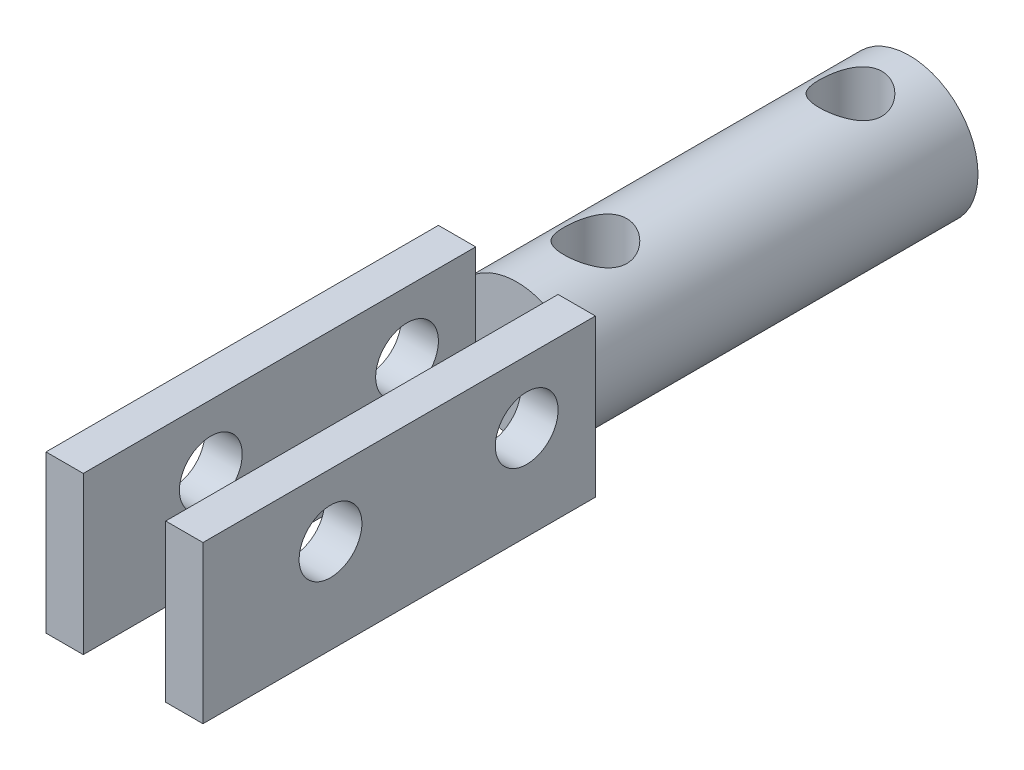
SolidWorks part; units mm, degrees
ref_plane "Plan de face" through (0, 0, 0) normal (0, 0, 1) x (1, 0, 0)
ref_plane "Plan de dessus" through (0, 0, 0) normal (0, 1, 0) x (1, 0, 0)
ref_plane "Plan de droite" through (0, 0, 0) normal (1, 0, 0) x (0, 0, -1)
sketch "Sketch1" plane through (0, 0, 0) normal (0, 0, 1) x (1, 0, 0)
  circle A0 centre (0, 0) radius 3.5
  dimension "D1" = 7
extrude "Boss-Extrude1" add sketch "Sketch1" along normal blind 20
sketch "Sketch2" plane through (0, 0, 0) normal (0, 1, 0) x (1, 0, 0)
  line L0 (3.5, 0) -> (-3.5, 0) construction
  circle A0 centre (0, -3) radius 1.6
  circle A1 centre (0, -16) radius 1.6
  dimension "D1" = 3.2
  dimension "D2" = 3.2
  dimension "D3" = 3
  dimension "D4" = 13
extrude "Cut-Extrude1" cut sketch "Sketch2" against normal through all and the other way through all
sketch "Sketch3" plane through (0, 0, 20) normal (0, 0, 1) x (1, 0, 0)
  line L1 (-4, -4) -> (4, -4)
  line L2 (-4, -4) -> (-4, 4)
  line L3 (-4, 4) -> (4, 4)
  line L4 (4, -4) -> (4, 4)
  circle A1 centre (0, 0) radius 3.5 construction
  dimension "D1" = 4
  dimension "D2" = 4
  dimension "D3" = 4
  dimension "D4" = 4
extrude "Boss-Extrude2" add sketch "Sketch3" along normal blind 20
sketch "Sketch4" plane through (0, 0, 40) normal (0, 0, 1) x (1, 0, 0)
  line L0 (-4, -4) -> (4, -4) construction
  line L1 (2.1, -4) -> (-2.1, -4)
  line L2 (2.1, -4) -> (2.1, 4)
  line L3 (2.1, 4) -> (-2.1, 4)
  line L4 (-2.1, -4) -> (-2.1, 4)
  line L5 (4, 4) -> (-4, 4) construction
  line L6 (-4, 4) -> (-4, -4) construction
  dimension "D1" = 4.2
  dimension "D2" = 1.9
extrude "Cut-Extrude2" cut sketch "Sketch4" against normal blind 20
sketch "Sketch5" plane through (-4, 0, 0) normal (-1, 0, 0) x (0, 0, 1)
  line L0 (20, 4) -> (20, -4) construction
  line L1 (40, 4) -> (20, 4) construction
  circle A0 centre (33.5, 0.8) radius 1.6
  circle A1 centre (23.5, 0.8) radius 1.6
  dimension "D1" = 3.2
  dimension "D2" = 3.2
  dimension "D3" = 10
  dimension "D4" = 3.5
  dimension "D5" = 3.2
extrude "Cut-Extrude3" cut sketch "Sketch5" against normal through all
